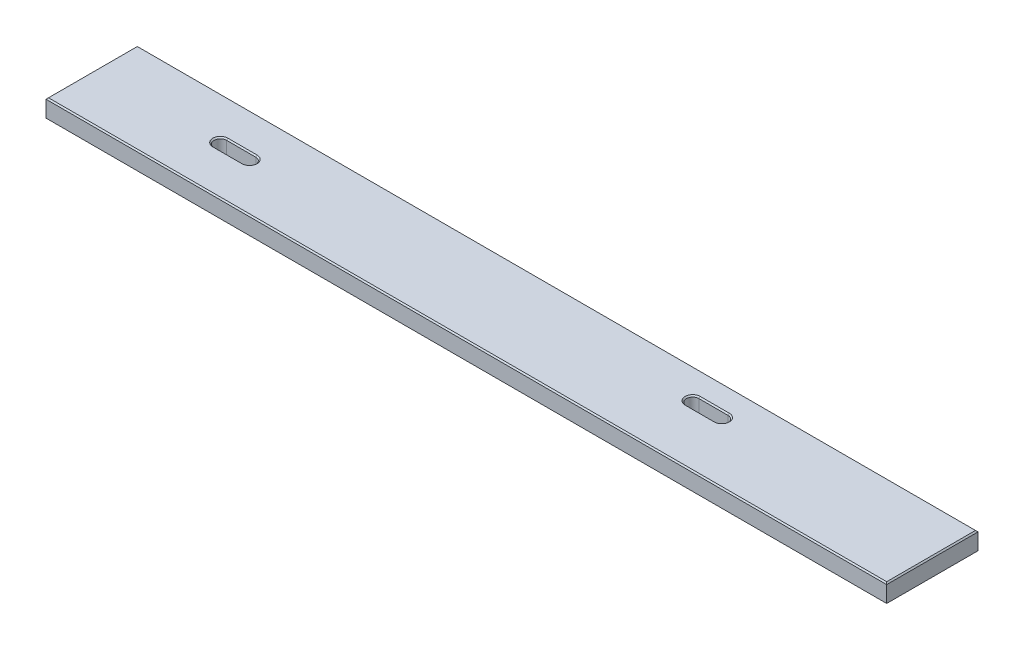
SolidWorks part; units mm, degrees
material "Oak"
ref_plane "Front Plane" through (0, 0, 0) normal (0, 0, 1) x (1, 0, 0)
ref_plane "Top Plane" through (0, 0, 0) normal (0, 1, 0) x (1, 0, 0)
ref_plane "Right Plane" through (0, 0, 0) normal (1, 0, 0) x (0, 0, -1)
sketch "Sketch1" plane through (0, 0, 0) normal (0, 1, 0) x (1, 0, 0)
  line L1 (0, 0) -> (1695.45, 0)
  line L2 (0, 0) -> (0, 184.15)
  line L3 (0, 184.15) -> (1695.45, 184.15)
  line L4 (1695.45, 0) -> (1695.45, 184.15)
  line L5 (1240.0153, 110.1661) -> (1181.2651, 110.1661)
  line L6 (254, 110.3186) -> (312.7502, 110.3186)
  line L8 (254, 84.9185) -> (312.7502, 84.9185)
  line L9 (1240.0153, 135.5661) -> (1181.2651, 135.5661)
  line L10 (1132.8767, 122.8661) -> (1477.331, 122.8661) construction
  arc A4 (312.7502, 84.9185) -> (312.7502, 110.3186) centre (312.7502, 97.6185) ccw
  arc A5 (254, 110.3186) -> (254, 84.9185) centre (254, 97.6185) ccw
  arc A6 (1240.0153, 135.5661) -> (1240.0153, 110.1661) centre (1240.0153, 122.8661) cw
  arc A7 (1181.2651, 110.1661) -> (1181.2651, 135.5661) centre (1181.2651, 122.8661) cw
  point P14 (312.7502, 110.3186)
  point P16 (1382.6998, 104.794)
  dimension "D7" = 12.7
  dimension "D6" = 122.8661
  dimension "D10" = 12.7
  dimension "D1" = 184.15
  dimension "D2" = 1695.45
  dimension "D3" = 58.7502
  dimension "D4" = 97.6185
  dimension "D5" = 254
  dimension "D8" = 1181.2651
  dimension "D9" = 58.7502
extrude "Boss-Extrude1" add sketch "Sketch1" along normal blind 38.1
chamfer "Chamfer1" distance 2.54 angle 45 12 edges at (847.725, 38.1, -184.15) (1695.45, 38.1, -92.075) (847.725, 38.1, 0) (0, 38.1, -92.075) (283.3751, 38.1, -110.3186) (283.3751, 38.1, -84.9185) (241.3, 38.1, -97.6185) (325.4502, 38.1, -97.6185) (1210.6402, 38.1, -135.5661) (1168.5651, 38.1, -122.8661) (1210.6402, 38.1, -110.1661) (1252.7153, 38.1, -122.8661)
chamfer "Chamfer2" distance 2.54 angle 45 12 edges at (283.3751, 0, -110.3186) (283.3751, 0, -84.9185) (847.725, 0, 0) (1695.45, 0, -92.075) (847.725, 0, -184.15) (0, 0, -92.075) (241.3, 0, -97.6185) (325.4502, 0, -97.6185) (1168.5651, 0, -122.8661) (1210.6402, 0, -135.5661) (1252.7153, 0, -122.8661) (1210.6402, 0, -110.1661)
sketch "Sketch2" plane through (0, 0, 0) normal (0, 1, 0) x (1, 0, 0)
  line L0 (254, 97.6185) -> (312.7502, 97.6185) construction
  line L1 (1181.2651, 122.8661) -> (1240.0153, 122.8661) construction
  circle A0 centre (283.3751, 97.6185) radius 19.05
  circle A1 centre (1210.6402, 122.8661) radius 19.05
  dimension "D1" = 38.1
  dimension "D2" = 38.1
extrude "Cut-Extrude1" cut sketch "Sketch2" along normal blind 3.175
